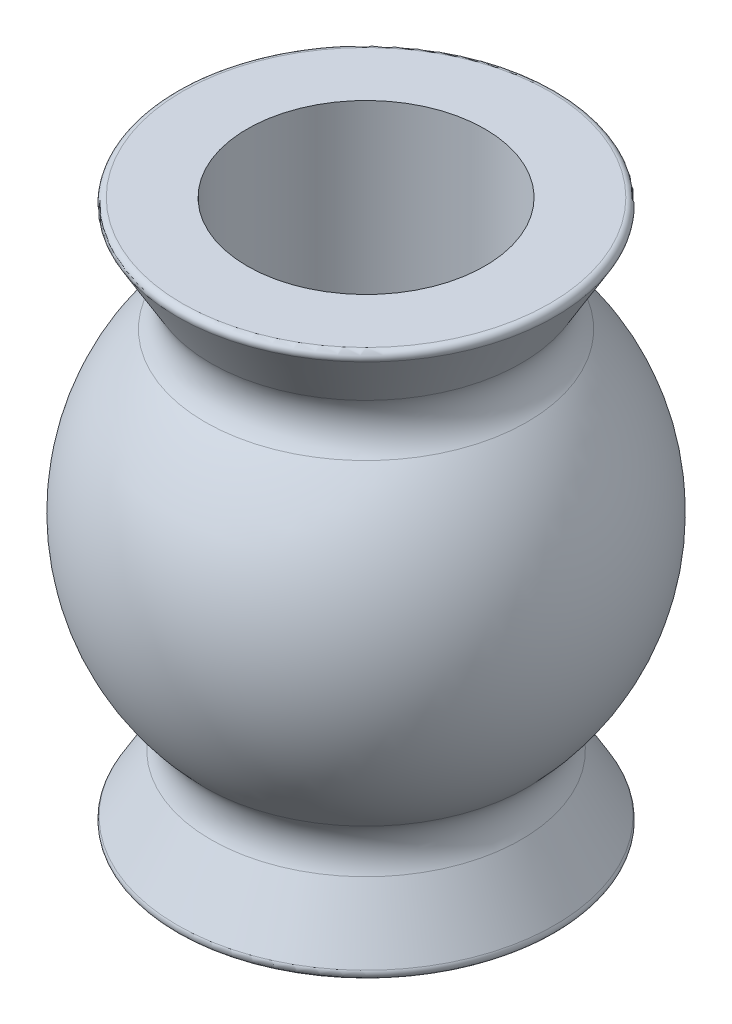
SolidWorks part; units mm, degrees
ref_plane "Front Plane" through (0, 0, 0) normal (0, 0, 1) x (1, 0, 0)
ref_plane "Top Plane" through (0, 0, 0) normal (0, 1, 0) x (1, 0, 0)
ref_plane "Right Plane" through (0, 0, 0) normal (1, 0, 0) x (0, 0, -1)
sketch "Sketch1" plane through (0, 0, 0) normal (0, 0, 1) x (1, 0, 0)
  line L0 (1.524, 0) -> (1.524, 6.985)
  line L1 (1.524, 6.985) -> (2.4892, 6.985)
  line L2 (2.4892, 6.985) -> (1.7773, 5.7785)
  line L3 (1.7773, 1.2065) -> (2.4892, 0)
  line L4 (2.4892, 0) -> (1.524, 0)
  line L5 (0, 0) -> (0, 7.7819) construction
  arc A0 (1.7773, 5.7785) -> (1.7773, 1.2065) centre (0, 3.4925) cw
  point P10 (1.524, 3.4925)
  dimension "D3" = 2.8956
  dimension "D1" = 3.048
  dimension "D2" = 6.985
  dimension "D4" = 4.9784
  dimension "D5" = 4.572
revolve "Revolve1" add sketch "Sketch1" angle 360 about L5
fillet "Fillet1" radius 0.508 2 edges at (0, 1.2065, -1.7773) (0, 5.7785, -1.7773)
fillet "Fillet2" radius 0.0762 2 edges at (0, 0, -2.4892) (0, 6.985, -2.4892)
sketch "Sketch3" plane through (0, 0, 0) normal (0, 0, 1) x (1, 0, 0)
  line L0 (0, 0) -> (0, 6.985) construction
  line L1 (1.524, 6.985) -> (-1.524, 6.985) construction
